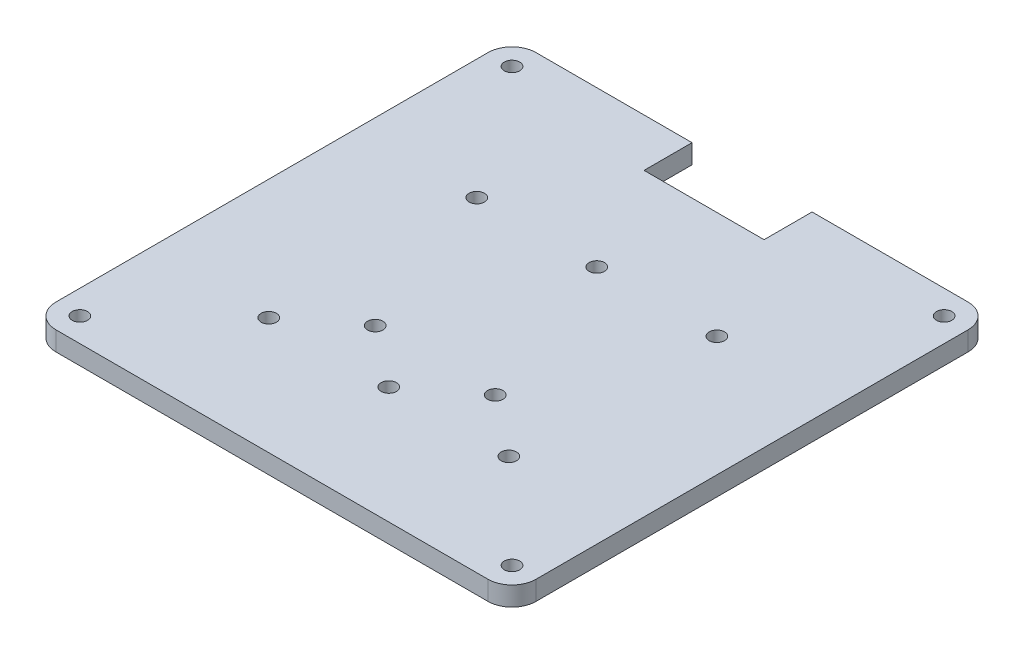
SolidWorks part; units mm, degrees
ref_plane "Front Plane" through (0, 0, 0) normal (0, 0, 1) x (1, 0, 0)
ref_plane "Top Plane" through (0, 0, 0) normal (0, 1, 0) x (1, 0, 0)
ref_plane "Right Plane" through (0, 0, 0) normal (1, 0, 0) x (0, 0, -1)
sketch "Sketch1" plane through (0, 0, 0) normal (0, 1, 0) x (1, 0, 0)
  line L1 (-45, -45) -> (45, -45) construction
  line L2 (-45, -45) -> (-45, 45) construction
  line L3 (-45, 45) -> (45, 45) construction
  line L4 (45, -45) -> (45, 45) construction
  line L5 (0, 45) -> (0, -45) construction
  line L6 (-45, 0) -> (45, 0) construction
  line L7 (50, -50) -> (-50, -50)
  line L8 (50, -50) -> (50, 50)
  line L9 (50, 50) -> (-50, 50)
  line L10 (-50, -50) -> (-50, 50)
  line L11 (0, 50) -> (0, -50) construction
  line L12 (50, 0) -> (-50, 0) construction
  line L13 (12.5, 40) -> (-12.5, 40)
  line L14 (12.5, 40) -> (12.5, 50)
  line L15 (12.5, 50) -> (-12.5, 50)
  line L16 (-12.5, 40) -> (-12.5, 50)
  line L17 (0, 50) -> (0, 40) construction
  line L18 (12.5, 45) -> (-12.5, 45) construction
  circle A0 centre (-45, 45) radius 1.6
  circle A1 centre (45, 45) radius 1.6
  circle A2 centre (45, -45) radius 1.6
  circle A3 centre (-45, -45) radius 1.6
  circle A4 centre (12.5, -16) radius 1.6
  circle A5 centre (-12.5, -16) radius 1.6
  circle A6 centre (0, -25.66) radius 1.6
  circle A7 centre (25, -25.66) radius 1.6
  circle A10 centre (0, 17.66) radius 1.6
  circle A11 centre (25, 17.66) radius 1.6
  circle A12 centre (-25, 17.66) radius 1.6
  circle A13 centre (-25, -25.66) radius 1.6
  point P0 (0, 0)
  point P4 (0, 0)
  dimension "D5" = 3.2
  dimension "D6" = 29
  dimension "D8" = 19.34
  dimension "D1" = 90
  dimension "D2" = 90
  dimension "D3" = 100
  dimension "D4" = 100
  dimension "D7" = 32.5
  dimension "D9" = 20
  dimension "D10" = 43.32
  dimension "D11" = 25
extrude "Boss-Extrude1" add sketch "Sketch1" along normal blind 4 contours L13 L16 L9 L10 L7 L8 L14 A12 A11 A10 A7 A6 A0 A1 A2 A3 A4 A5 A13
fillet "Fillet1" radius 5 4 edges at (-50, 2, -50) (50, 2, -50) (50, 2, 50) (-50, 2, 50)
